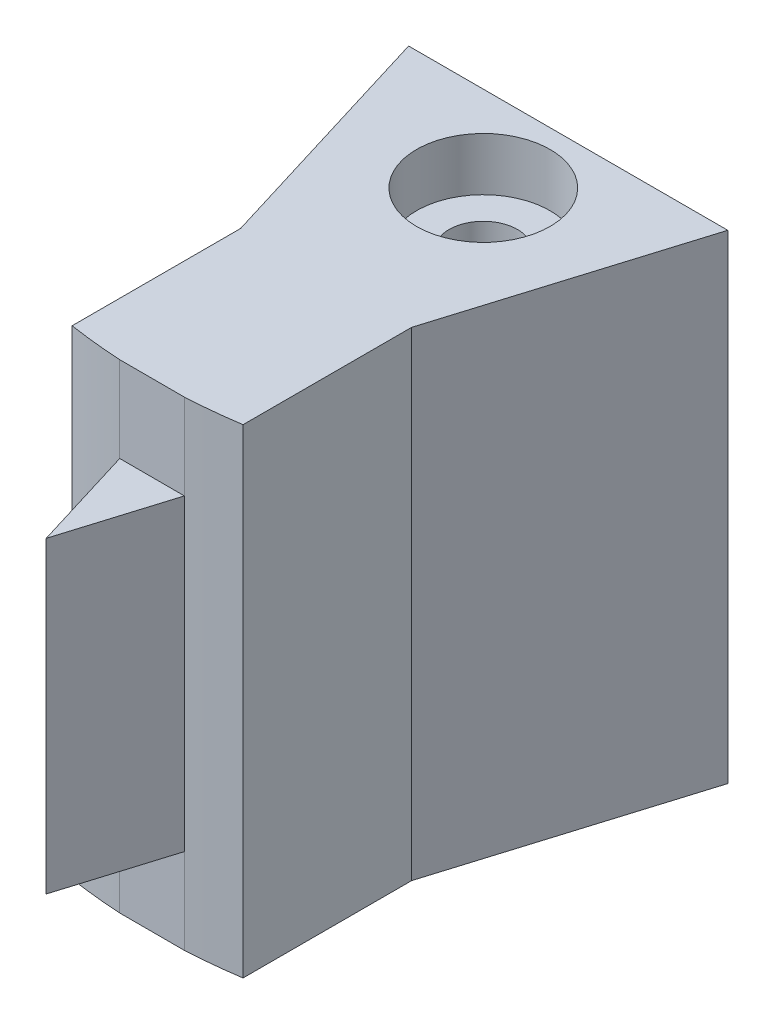
SolidWorks part; units mm, degrees
material "Plain Carbon Steel"
ref_plane "Front Plane" through (0, 0, 0) normal (0, 0, 1) x (1, 0, 0)
ref_plane "Top Plane" through (0, 0, 0) normal (0, 1, 0) x (1, 0, 0)
ref_plane "Right Plane" through (0, 0, 0) normal (1, 0, 0) x (0, 0, -1)
sketch "Sketch1" plane through (0, 0, 0) normal (0, 1, 0) x (1, 0, 0)
  line L0 (4.6424, -4.5654) -> (-4.6824, -4.5654)
  line L1 (-2.52, -11.6382) -> (-4.6824, -4.5654)
  line L2 (-0.02, -19.8154) -> (-0.02, -4.5654) construction
  line L3 (2.48, -11.6382) -> (4.6424, -4.5654)
  line L6 (-2.52, -16.5593) -> (-2.52, -11.6382)
  line L7 (2.48, -16.5654) -> (2.48, -11.6382)
  line L8 (0.925, -16.7244) -> (-0.02, -19.8154)
  line L9 (-0.02, -19.8154) -> (-0.9657, -16.7221)
  arc A0 (-2.52, -16.5593) -> (-0.9657, -16.7221) centre (0, 0) ccw
  arc A1 (0.925, -16.7244) -> (2.48, -16.5654) centre (0, 0) ccw
  point P2 (-0.02, -16.5654)
  point P8 (-0.0154, 5.3291)
  dimension "D1" = 17
  dimension "D2" = 3.25
  dimension "D3" = 12
  dimension "D6" = 17
extrude "Boss-Extrude1" add sketch "Sketch1" along normal blind 12 and the other way blind 2
sketch "Sketch2" plane through (0, 0, 4.5654) normal (0, 0, -1) x (-1, 0, 0)
  line L0 (-4.6424, 12) -> (4.6824, -2) construction
  line L1 (4.6824, 12) -> (-4.6424, -2) construction
  line L3 (-2.8782, 5.95) -> (2.9183, 5.95)
  line L5 (-2.8782, 4.05) -> (2.9183, 4.05)
  arc A0 (-2.8782, 4.05) -> (2.9183, 4.05) centre (0.02, 5) ccw
  arc A1 (2.9183, 5.95) -> (-2.8782, 5.95) centre (0.02, 5) ccw
  dimension "D1" = 1.9
extrude "Cut-Extrude1" cut sketch "Sketch2" against normal blind 5
ref_plane "Plane2" through (0, 0, 10.0654) normal (0, 0, -1) x (-1, 0, 0)
ref_plane "Plane4" through (0, 0, 10.0654) normal (0, 0, -1) x (-1, 0, 0)
sketch "Sketch5" plane through (0, 5.74, 0) normal (0, 1, 0) x (1, 0, 0)
  line L3 (0.9955, -10.0654) -> (-0.9955, -10.0654) construction
  line L4 (4.6424, -4.5654) -> (-4.6824, -4.5654) construction
  circle A0 centre (0, -7.0654) radius 1
  dimension "D1" = 3
  dimension "D2" = 2.5
extrude "Cut-Extrude2" cut sketch "Sketch5" against normal through all and the other way through all
sketch "Sketch6" plane through (0, 12, 0) normal (0, 1, 0) x (1, 0, 0)
  circle A0 centre (0, -7.0654) radius 1.95
extrude "Cut-Extrude3" cut sketch "Sketch6" against normal blind 1.55 contours A0
sketch "Sketch7" plane through (0, 12, 0) normal (0, 1, 0) x (1, 0, 0)
  line L0 (0.925, -16.7244) -> (-0.02, -19.8154)
  line L1 (-0.02, -19.8154) -> (-0.9657, -16.7221)
  line L2 (-0.9657, -16.7221) -> (0.925, -16.7244)
extrude "Cut-Extrude4" cut sketch "Sketch7" against normal blind 2.5
ref_plane "Plane5" through (0, 5, 0) normal (0, 1, 0) x (1, 0, 0)
mirror "Mirror1" about plane through (0, 5, 0) normal (0, 1, 0) of "Cut-Extrude4"
